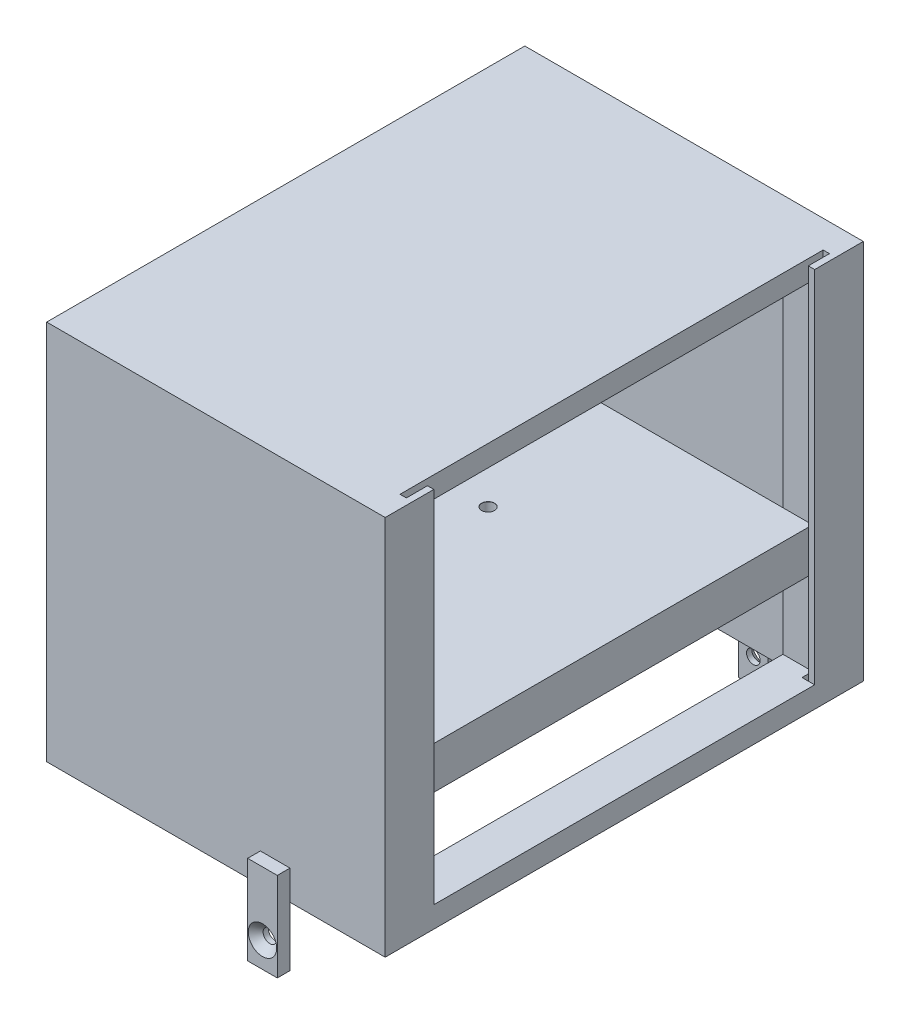
SolidWorks part; units mm, degrees
ref_plane "Front Plane" through (0, 0, 0) normal (0, 0, 1) x (1, 0, 0)
ref_plane "Top Plane" through (0, 0, 0) normal (0, 1, 0) x (1, 0, 0)
ref_plane "Right Plane" through (0, 0, 0) normal (1, 0, 0) x (0, 0, -1)
sketch "Sketch1" plane through (0, 0, 0) normal (0, 1, 0) x (1, 0, 0)
  line L1 (-40, -56.5) -> (40, -56.5)
  line L2 (-40, -56.5) -> (-40, 56.5)
  line L3 (-40, 56.5) -> (40, 56.5)
  line L4 (40, -56.5) -> (40, 56.5)
  line L5 (-40, -56.5) -> (40, 56.5) construction
  line L6 (-40, 56.5) -> (40, -56.5) construction
  point P0 (0, 0)
  dimension "D1" = 80
  dimension "D2" = 113
extrude "Boss-Extrude1" add sketch "Sketch1" along normal blind 90
sketch "Sketch3" plane through (0, 0, 0) normal (0, -1, 0) x (1, 0, 0)
  line L0 (40, 56.5) -> (40, -56.5) construction
  line L1 (-25, -50) -> (30, -50)
  line L2 (-25, -50) -> (-25, 50)
  line L3 (-25, 50) -> (30, 50)
  line L4 (30, -50) -> (30, 50)
  line L5 (40, -56.5) -> (-40, -56.5) construction
  dimension "D1" = 100
  dimension "D2" = 55
  dimension "D3" = 10
  dimension "D4" = 6.5
extrude "Cut-Extrude2" cut sketch "Sketch3" against normal blind 87
sketch "Sketch4" plane through (-40, 0, 0) normal (-1, 0, 0) x (0, 0, 1)
  line L1 (-47.5, 5) -> (47.5, 5)
  line L2 (-47.5, 5) -> (-47.5, 85)
  line L3 (-47.5, 85) -> (47.5, 85)
  line L4 (47.5, 5) -> (47.5, 85)
  line L6 (-56.5, 0) -> (56.5, 0) construction
  point P6 (0, 85)
  dimension "D1" = 80
  dimension "D2" = 95
  dimension "D3" = 5
extrude "Cut-Extrude3" cut sketch "Sketch4" against normal blind 77 contours L2 L3 L4 L1
sketch "Sketch6" plane through (37, 0, 0) normal (-1, 0, 0) x (0, 0, 1)
  line L0 (-47.5, 5) -> (-47.5, 85) construction
  line L1 (-47.5, 25) -> (47.5, 25)
  line L2 (-47.5, 25) -> (-47.5, 35)
  line L3 (-47.5, 35) -> (47.5, 35)
  line L4 (47.5, 25) -> (47.5, 35)
  line L5 (47.5, 5) -> (47.5, 85) construction
  line L6 (-47.5, 85) -> (47.5, 85) construction
  dimension "D1" = 10
  dimension "D2" = 50
extrude "Boss-Extrude4" add sketch "Sketch6" along normal blind 77
sketch "Sketch7" plane through (0, 0, 0) normal (0, 1, 0) x (1, 0, 0)
  line L0 (40, 45) -> (38.5, 45)
  line L1 (40, -56.5) -> (40, 56.5) construction
  line L2 (38.5, 45) -> (38.5, 50)
  line L3 (38.5, 50) -> (37, 50)
  line L4 (37, 50) -> (37, -50)
  line L5 (37, -50) -> (38.5, -50)
  line L6 (38.5, -50) -> (38.5, -45)
  line L7 (38.5, -45) -> (40, -45)
  line L8 (40, -45) -> (40, 45)
  point P4 (37, 0)
  dimension "D1" = 1.5
  dimension "D2" = 1.5
  dimension "D3" = 100
  dimension "D4" = 1.5
  dimension "D5" = 90
  dimension "D6" = 5
  dimension "D7" = 5
extrude "Cut-Extrude4" cut sketch "Sketch7" along normal through all
sketch "Sketch8" plane through (0, 35, 0) normal (0, 1, 0) x (1, 0, 0)
  line L0 (37, 50) -> (37, -50) construction
  line L2 (-40, -56.5) -> (40, -56.5) construction
  circle A0 centre (-5.02, -17.05) radius 1.5
  circle A1 centre (-5.02, 12.84) radius 1.5
  circle A2 centre (-29.68, 12.84) radius 1.5
  circle A3 centre (-29.68, -17.05) radius 1.5
  dimension "D3" = 3
  dimension "D8" = 3
  dimension "D9" = 3
  dimension "D10" = 3
  dimension "D1" = 42.02
  dimension "D2" = 39.45
  dimension "D4" = 29.89
  dimension "D5" = 24.66
  dimension "D6" = 24.66
  dimension "D7" = 29.89
  dimension "D11" = 42.02
hole_wizard "Ø3.0 (3) Diameter Hole1" positions "Sketch9" profile "Sketch10" hole size "Ø3.0" standard "ISO"
sketch "Sketch9" plane through (0, 35, 0) normal (0, 1, 0) x (1, 0, 0)
  point P0 (-5.02, -17.05)
  point P4 (-5.02, 12.84)
  point P7 (-29.68, 12.84)
  point P10 (-29.68, -17.05)
sketch "Sketch10" plane through (-5.02, 35, 17.05) normal (1, 0, 0) x (0, 0, 1)
  line L0 (0, 0) -> (0, 6)
  line L1 (0, 6) -> (1.5, 5.0987)
  line L2 (1.5, 5.0987) -> (1.5, 0.025)
  line L3 (1.5, 0.025) -> (1.525, 0)
  line L5 (1.525, 0) -> (0, 0)
  line L6 (-1.5, 0.025) -> (-1.525, 0) construction
  line L10 (0, 6) -> (-1.5, 5.0987) construction
  line L11 (0, -6.35) -> (0, 107.95) construction
  dimension "Hole Dia." = 3
  dimension "Hole Depth" = 6
  dimension "Near C'Sink Dia." = 3.05
  dimension "Near C'Sink Angle" = 90
  dimension "Drill Angle" = 118
sketch "Sketch11" plane through (37, 0, 0) normal (1, 0, 0) x (0, 0, -1)
  line L0 (45, 90) -> (45, 0) construction
  line L1 (-45, 0) -> (45, 0)
  line L2 (-45, 0) -> (-45, 5)
  line L3 (-45, 5) -> (45, 5)
  line L4 (45, 0) -> (45, 5)
  dimension "D1" = 5
extrude "Boss-Extrude5" add sketch "Sketch11" along normal through all
sketch "Sketch12" plane through (0, 0, 56.5) normal (0, 0, 1) x (1, 0, 0)
  line L1 (10.5, 7) -> (17.5, 7)
  line L2 (10.5, 7) -> (10.5, -14)
  line L3 (10.5, -14) -> (17.5, -14)
  line L4 (17.5, 7) -> (17.5, -14)
  line L5 (10.5, 7) -> (17.5, -14) construction
  line L6 (10.5, -14) -> (17.5, 7) construction
  line L7 (40, 90) -> (40, 0) construction
  line L8 (-40, 0) -> (40, 0) construction
  point P0 (14, -3.5)
  dimension "D1" = 22.5
  dimension "D2" = 7
  dimension "D3" = 7
  dimension "D4" = 21
extrude "Boss-Extrude6" add sketch "Sketch12" along normal blind 3
sketch "Sketch13" plane through (0, 0, -56.5) normal (0, 0, -1) x (-1, 0, 0)
  line L0 (-40, 90) -> (-40, 0) construction
  line L1 (-10.5, 7) -> (-17.5, 7)
  line L2 (-10.5, 7) -> (-10.5, -14)
  line L3 (-10.5, -14) -> (-17.5, -14)
  line L4 (-17.5, 7) -> (-17.5, -14)
  line L5 (-10.5, 7) -> (-17.5, -14) construction
  line L6 (-10.5, -14) -> (-17.5, 7) construction
  line L7 (-40, 0) -> (40, 0) construction
  point P0 (-14, -3.5)
  dimension "D1" = 22.5
  dimension "D2" = 7
  dimension "D3" = 21
  dimension "D4" = 7
extrude "Boss-Extrude7" add sketch "Sketch13" along normal blind 3
hole_wizard "CSK for M3 Hex Socket Countersunk Cap Screw1" positions "Sketch14" profile "Sketch15" countersink size "M3" standard "ISO"
sketch "Sketch14" plane through (0, 0, -59.5) normal (0, 0, -1) x (-1, 0, 0)
  line L0 (-10.5, 0) -> (40, 0) construction
  line L2 (-17.5, 7) -> (-17.5, -14) construction
  point P0 (-14, -8)
  dimension "D1" = 8
  dimension "D2" = 3.5
sketch "Sketch15" plane through (14, -8, -59.5) normal (1, 0, 0) x (0, 1, 0)
  line L0 (0, 0) -> (0, 8.2)
  line L1 (0, 8.2) -> (1.6, 7.2386)
  line L2 (1.6, 7.2386) -> (1.6, 1.76)
  line L3 (1.6, 1.76) -> (3.36, 0)
  line L5 (3.36, 0) -> (0, 0)
  line L6 (-1.6, 1.76) -> (-3.36, 0) construction
  line L10 (0, 8.2) -> (-1.6, 7.2386) construction
  line L11 (0, -6.35) -> (0, 107.95) construction
  dimension "Hole Dia." = 3.2
  dimension "Hole Depth" = 8.2
  dimension "Near C'Sink Dia." = 6.72
  dimension "Near C'Sink Angle" = 90
  dimension "Drill Angle" = 118
hole_wizard "CSK for M3 Hex Socket Countersunk Cap Screw2" positions "Sketch16" profile "Sketch17" countersink size "M3" standard "ISO"
sketch "Sketch16" plane through (0, 0, 59.5) normal (0, 0, 1) x (1, 0, 0)
  line L0 (17.5, 0) -> (40, 0) construction
  line L1 (17.5, -14) -> (17.5, 7) construction
  point P0 (14, -8)
  dimension "D1" = 8
  dimension "D2" = 3.5
sketch "Sketch17" plane through (14, -8, 59.5) normal (1, 0, 0) x (0, -1, 0)
  line L0 (0, 0) -> (0, 8.2)
  line L1 (0, 8.2) -> (1.6, 7.2386)
  line L2 (1.6, 7.2386) -> (1.6, 1.76)
  line L3 (1.6, 1.76) -> (3.36, 0)
  line L5 (3.36, 0) -> (0, 0)
  line L6 (-1.6, 1.76) -> (-3.36, 0) construction
  line L10 (0, 8.2) -> (-1.6, 7.2386) construction
  line L11 (0, -6.35) -> (0, 107.95) construction
  dimension "Hole Dia." = 3.2
  dimension "Hole Depth" = 8.2
  dimension "Near C'Sink Dia." = 6.72
  dimension "Near C'Sink Angle" = 90
  dimension "Drill Angle" = 118
